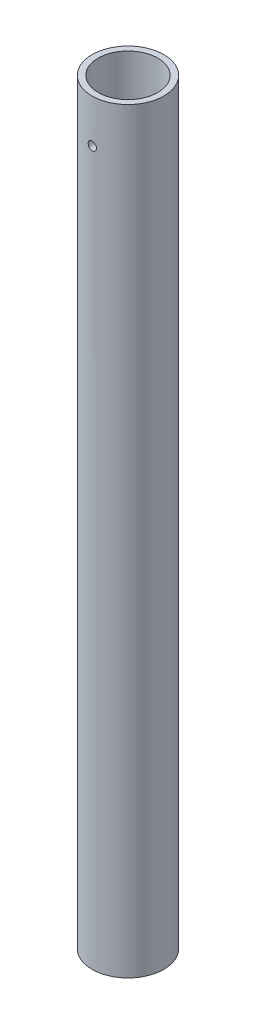
SolidWorks part; units mm, degrees
material "6061 Alloy"
ref_plane "Front Plane" through (0, 0, 0) normal (0, 0, 1) x (1, 0, 0)
ref_plane "Top Plane" through (0, 0, 0) normal (0, 1, 0) x (1, 0, 0)
ref_plane "Right Plane" through (0, 0, 0) normal (1, 0, 0) x (0, 0, -1)
sketch "Sketch1" plane through (0, 0, 0) normal (0, 1, 0) x (1, 0, 0)
  circle A0 centre (0, 0) radius 21.082
  circle A1 centre (0, 0) radius 17.526
  dimension "D1" = 42.164
  dimension "D2" = 35.052
extrude "Boss-Extrude1" add sketch "Sketch1" along normal blind 444.5
ref_plane "Plane1" through (0, 0, 21.082) normal (0, 0, 1) x (1, 0, 0)
hole_wizard "#10 (0.1935) Diameter Hole1" positions "Sketch2" profile "Sketch3" hole size "#10" standard "ANSI Inch" end condition through all
sketch "Sketch2" plane through (0, 0, 21.082) normal (0, 0, 1) x (1, 0, 0)
  line L0 (17.526, 444.5) -> (-17.526, 444.5) construction
  point P0 (0, 419.1)
  dimension "D1" = 25.4
sketch "Sketch3" plane through (0, 419.1, 21.082) normal (1, 0, 0) x (0, -1, 0)
  line L0 (0, 0) -> (0, 42.164)
  line L1 (0, 42.164) -> (2.4574, 42.164)
  line L2 (2.4574, 42.164) -> (2.4574, 0)
  line L5 (2.4574, 0) -> (0, 0)
  line L11 (0, -6.35) -> (0, 107.95) construction
  dimension "Thru Hole Dia." = 4.9149
  dimension "Thru Hole Depth" = 42.164
